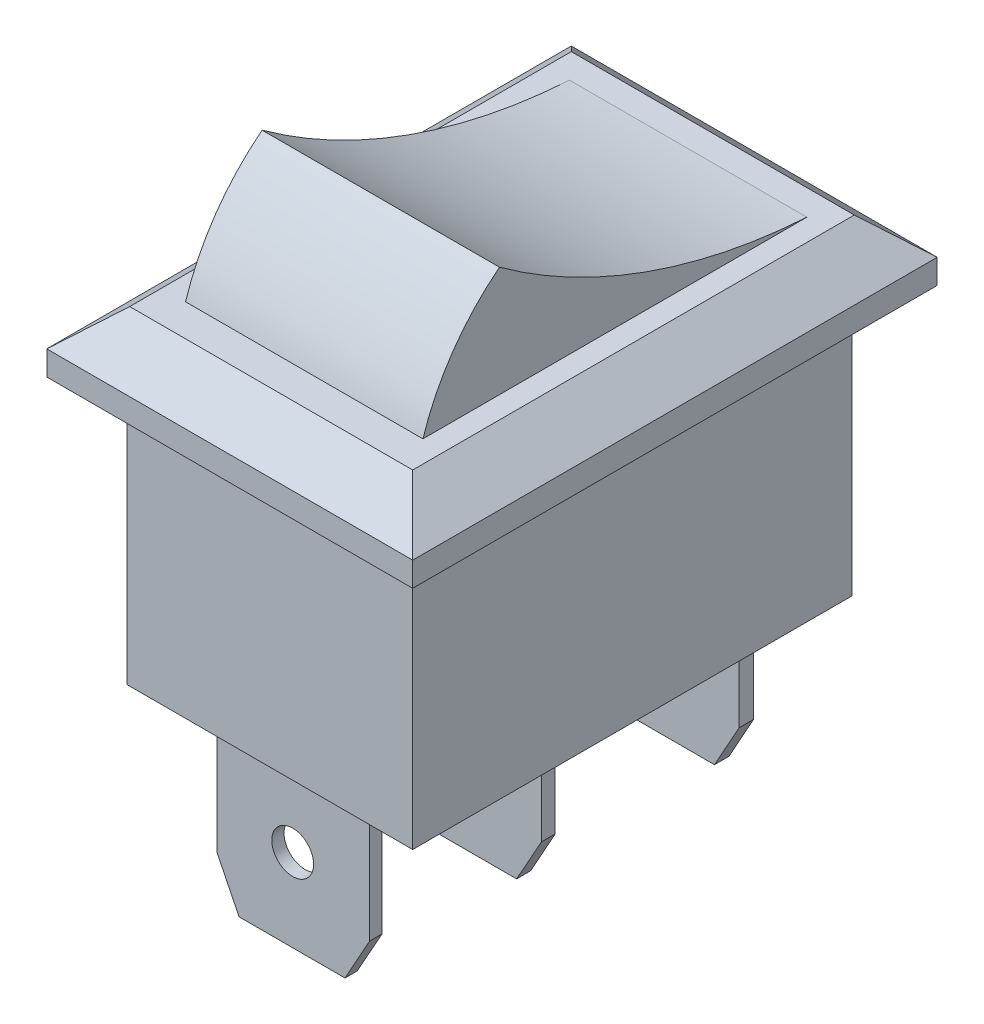
SolidWorks part; units mm, degrees
ref_plane "Front Plane" through (0, 0, 0) normal (0, 0, 1) x (1, 0, 0)
ref_plane "Top Plane" through (0, 0, 0) normal (0, 1, 0) x (1, 0, 0)
ref_plane "Right Plane" through (0, 0, 0) normal (1, 0, 0) x (0, 0, -1)
sketch "Sketch1" plane through (0, 0, 0) normal (0, 1, 0) x (1, 0, 0)
  line L1 (-6.0984, 5.5467) -> (8.9016, 5.5467)
  line L2 (-6.0984, 5.5467) -> (-6.0984, -15.9533)
  line L3 (-6.0984, -15.9533) -> (8.9016, -15.9533)
  line L4 (8.9016, 5.5467) -> (8.9016, -15.9533)
  dimension "D1" = 15
  dimension "D2" = 21.5
extrude "Boss-Extrude1" add sketch "Sketch1" along normal blind 2.5
chamfer "Chamfer1" distance 1.5 distance2 1.7 4 edges at (1.4016, 2.5, -5.5467) (8.9016, 2.5, 5.2033) (1.4016, 2.5, 15.9533) (-6.0984, 2.5, 5.2033)
sketch "Sketch3" plane through (0, 0, 0) normal (0, -1, 0) x (1, 0, 0)
  line L1 (-4.5255, 14.227) -> (7.1745, 14.227)
  line L2 (-4.5255, 14.227) -> (-4.5255, -3.773)
  line L3 (-4.5255, -3.773) -> (7.1745, -3.773)
  line L4 (7.1745, 14.227) -> (7.1745, -3.773)
  dimension "D1" = 11.7
  dimension "D2" = 18
extrude "Boss-Extrude2" add sketch "Sketch3" along normal blind 11 contours L2 L1 L4 L3
sketch "Sketch4" plane through (0, -11, 0) normal (0, -1, 0) x (1, 0, 0)
  line L1 (-1.8989, 13.1746) -> (4.3594, 13.1746)
  line L2 (-1.8989, 13.1746) -> (-1.8989, 12.6721)
  line L3 (-1.8989, 12.6721) -> (4.3594, 12.6721)
  line L4 (4.3594, 13.1746) -> (4.3594, 12.6721)
  line L5 (-1.8989, 6.1397) -> (4.3594, 6.1397)
  line L6 (-1.8989, 6.1397) -> (-1.8989, 5.5687)
  line L7 (-1.8989, 5.5687) -> (4.3594, 5.5687)
  line L8 (4.3594, 6.1397) -> (4.3594, 5.5687)
  line L9 (-1.8989, -1.9686) -> (4.3594, -1.9686)
  line L10 (-1.8989, -1.9686) -> (-1.8989, -2.5625)
  line L11 (-1.8989, -2.5625) -> (4.3594, -2.5625)
  line L12 (4.3594, -1.9686) -> (4.3594, -2.5625)
extrude "Boss-Extrude3" add sketch "Sketch4" along normal blind 7
sketch "Sketch5" plane through (0, 0, -2.5625) normal (0, 0, -1) x (-1, 0, 0)
  line L0 (-3.0092, -18.6074) -> (-4.8895, -15.2328)
  line L1 (-4.8895, -15.2328) -> (-5.1759, -18.4829)
  line L2 (-5.1759, -18.4829) -> (-3.0092, -18.6074)
  line L3 (0.7265, -18.5452) -> (2.3578, -15.2328)
  line L4 (2.3578, -15.2328) -> (2.8185, -18.5452)
  line L5 (2.8185, -18.5452) -> (0.7265, -18.5452)
  circle A0 centre (-1.2036, -14.6102) radius 0.8578
extrude "Cut-Extrude1" cut sketch "Sketch5" against normal blind 22
sketch "Sketch7" plane through (-6.0984, 0, 0) normal (-1, 0, 0) x (0, 0, 1)
  line L0 (-3.8467, 2.5) -> (14.2533, 2.5) construction
  line L1 (12.939, 2.5) -> (-2.7975, 2.5)
  arc A0 (-2.7975, 2.5) -> (9.8021, 7.0249) centre (-4.2739, 26.415) ccw
  arc A1 (9.8021, 7.0249) -> (12.939, 2.5) centre (4.0099, -0.3404) cw
extrude "Boss-Extrude4" add sketch "Sketch7" against normal blind 22
sketch "Sketch8" plane through (0, 2.5, 0) normal (0, 1, 0) x (1, 0, 0)
  line L0 (7.2016, 2.7975) -> (-4.3984, 2.7975) construction
  line L1 (-3.4237, 2.7975) -> (-9.7277, 2.7975)
  line L2 (-3.4237, 2.7975) -> (-3.4237, -13.9055)
  line L3 (-3.4237, -13.9055) -> (-9.7277, -13.9055)
  line L4 (-9.7277, 2.7975) -> (-9.7277, -13.9055)
  line L6 (6.3063, 2.7975) -> (19.1883, 2.7975)
  line L7 (6.3063, 2.7975) -> (6.3063, -14.4537)
  line L8 (6.3063, -14.4537) -> (19.1883, -14.4537)
  line L9 (19.1883, 2.7975) -> (19.1883, -14.4537)
extrude "Cut-Extrude2" cut sketch "Sketch8" along normal blind 16
